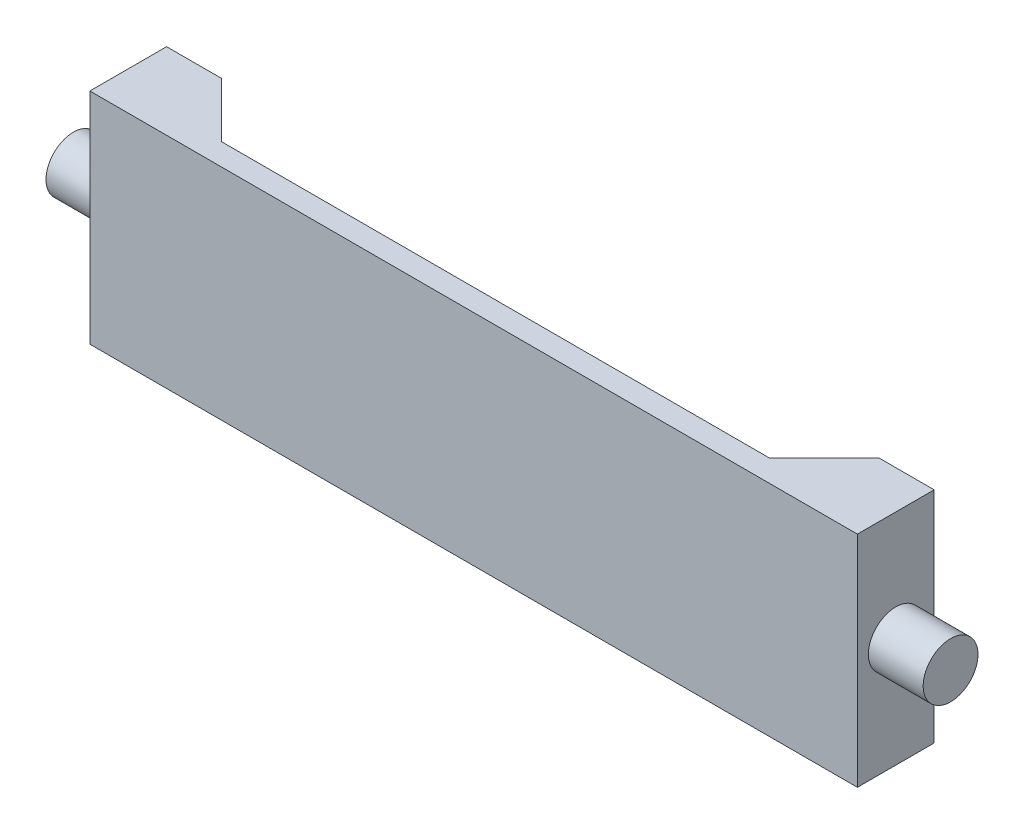
SolidWorks part; units mm, degrees
ref_plane "Front Plane" through (0, 0, 0) normal (0, 0, 1) x (1, 0, 0)
ref_plane "Top Plane" through (0, 0, 0) normal (0, 1, 0) x (1, 0, 0)
ref_plane "Right Plane" through (0, 0, 0) normal (1, 0, 0) x (0, 0, -1)
sketch "Sketch1" plane through (0, 0, 0) normal (0, 0, 1) x (1, 0, 0)
  line L1 (-350, -100) -> (350, -100)
  line L2 (-350, -100) -> (-350, 100)
  line L3 (-350, 100) -> (350, 100)
  line L4 (350, -100) -> (350, 100)
  line L5 (-350, -100) -> (350, 100) construction
  line L6 (-350, 100) -> (350, -100) construction
  point P0 (0, 0)
  dimension "D1" = 700
  dimension "D2" = 200
extrude "Boss-Extrude1" add sketch "Sketch1" along normal blind 70
sketch "Sketch2" plane through (0, -100, 0) normal (0, -1, 0) x (1, 0, 0)
  line L0 (-350, 0) -> (-300, 0) construction
  line L1 (-350, 0) -> (350, 0) construction
  line L2 (-300, 0) -> (-250, 50)
  line L3 (-250, 50) -> (250, 50)
  line L4 (250, 50) -> (300, 0)
  line L5 (300, 0) -> (350, 0) construction
  line L6 (-300, 0) -> (300, 0)
  dimension "D1" = 50
  dimension "D2" = 50
  dimension "D3" = 50
  dimension "D4" = 50
extrude "Cut-Extrude1" cut sketch "Sketch2" against normal through all
sketch "Sketch3" plane through (-350, 0, 0) normal (-1, 0, 0) x (0, 0, 1)
  line L0 (0, 0) -> (70, 0) construction
  line L1 (0, 100) -> (0, -100) construction
  line L2 (70, 100) -> (70, -100) construction
  circle A0 centre (35, 0) radius 25
  dimension "D1" = 50
extrude "Boss-Extrude2" add sketch "Sketch3" along normal blind 50
sketch "Sketch4" plane through (350, 0, 0) normal (1, 0, 0) x (0, 0, -1)
  circle A1 centre (-35, 0) radius 25
  circle A2 centre (-35, 0) radius 25
  dimension "D1" = 0
extrude "Boss-Extrude3" add sketch "Sketch4" along normal blind 50
